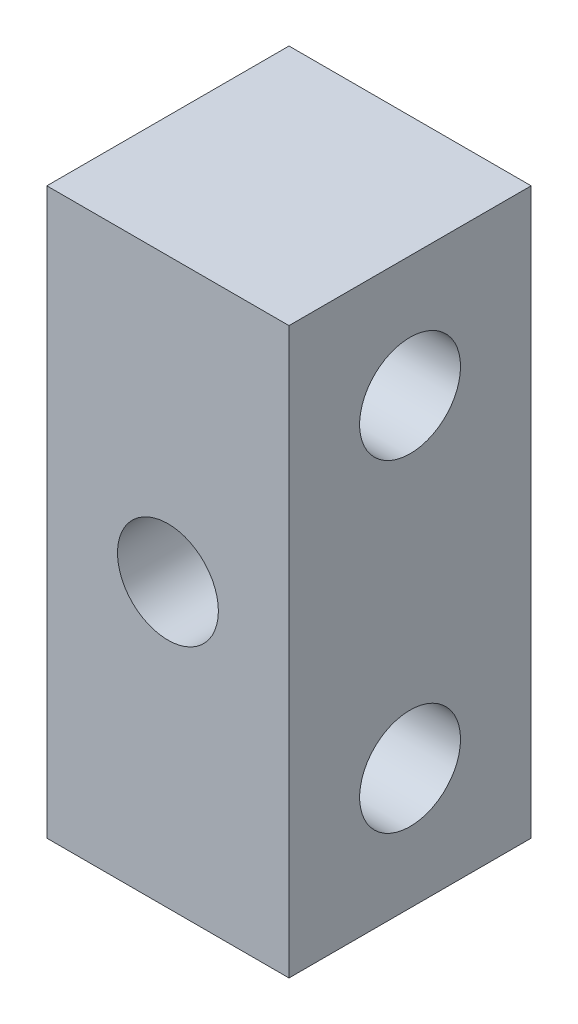
SolidWorks part; units mm, degrees
material "6061 合金"
ref_plane "前视基准面" through (0, 0, 0) normal (0, 0, 1) x (1, 0, 0)
ref_plane "上视基准面" through (0, 0, 0) normal (0, 1, 0) x (1, 0, 0)
ref_plane "右视基准面" through (0, 0, 0) normal (1, 0, 0) x (0, 0, -1)
sketch "草图1" plane through (0, 0, 0) normal (1, 0, 0) x (0, 0, -1)
  line L0 (0, 0) -> (3, 0) construction
  line L1 (-3, 7) -> (3, 7)
  line L2 (-3, 7) -> (-3, -7)
  line L3 (-3, -7) -> (3, -7)
  line L4 (3, 7) -> (3, -7)
  line L5 (-3, 7) -> (3, -7) construction
  line L6 (-3, -7) -> (3, 7) construction
  circle A0 centre (0, 4) radius 1.25
  circle A1 centre (0, -4) radius 1.25
  point P0 (0, 0)
  dimension "D1" = 2.5
  dimension "D2" = 8
  dimension "D3" = 6
  dimension "D4" = 3
extrude "凸台-拉伸1" add sketch "草图1" along normal blind 6
cosmetic thread "装饰螺纹线1"
cosmetic thread "装饰螺纹线2"
sketch "草图2" plane through (0, 0, 3) normal (0, 0, 1) x (1, 0, 0)
  line L0 (3, 7) -> (3, -7) construction
  line L1 (6, 7) -> (0, 7) construction
  line L2 (6, -7) -> (0, -7) construction
  circle A0 centre (3, 0) radius 1.25
  dimension "D1" = 2.5
extrude "切除-拉伸1" cut sketch "草图2" against normal through all
cosmetic thread "装饰螺纹线3" parameters "D2"=3
